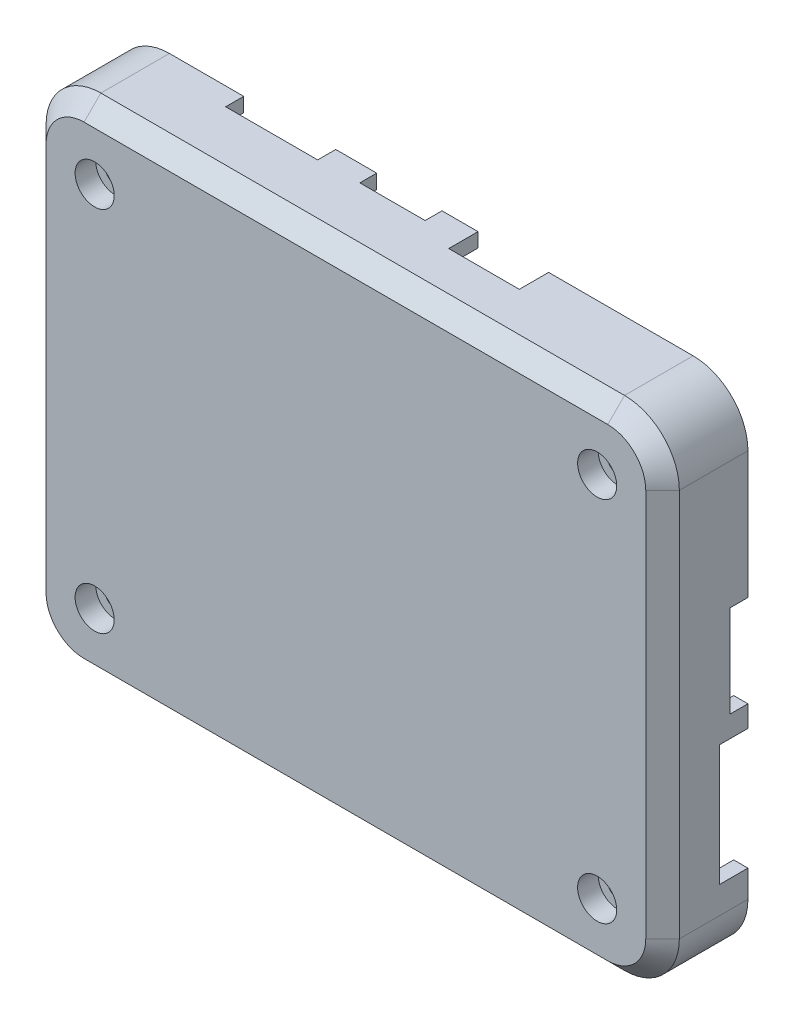
SolidWorks part; units mm, degrees
material "ABS"
ref_plane "前基準面" through (0, 0, 0) normal (0, 0, 1) x (1, 0, 0)
ref_plane "上基準面" through (0, 0, 0) normal (0, 1, 0) x (1, 0, 0)
ref_plane "右基準面" through (0, 0, 0) normal (1, 0, 0) x (0, 0, -1)
sketch "草圖1" plane through (0, 0, 0) normal (0, 0, 1) x (1, 0, 0)
  line L1 (-44.5, 35) -> (44.5, 35)
  line L2 (-44.5, 35) -> (-44.5, -35)
  line L3 (-44.5, -35) -> (44.5, -35)
  line L4 (44.5, 35) -> (44.5, -35)
  line L5 (-44.5, 35) -> (44.5, -35) construction
  line L6 (-44.5, -35) -> (44.5, 35) construction
  point P0 (0, 0)
  dimension "D1" = 89
  dimension "D2" = 70
extrude "填料-伸長1" add sketch "草圖1" along normal blind 12
fillet "圓角1" radius 7.7 4 edges at (-44.5, -35, 6) (44.5, -35, 6) (44.5, 35, 6) (-44.5, 35, 6)
chamfer "導角1" distance 2.36 angle 45 8 edges at (0, -35, 12) (42.2447, -32.7447, 12) (-42.2447, -32.7447, 12) (44.5, 0, 12) (-44.5, 0, 12) (42.2447, 32.7447, 12) (-42.2447, 32.7447, 12) (0, 35, 12)
shell "薄殼1" thickness 2
sketch "草圖2" plane through (0, 35, 0) normal (0, 1, 0) x (1, 0, 0)
  line L0 (36.8, 0) -> (-36.8, 0) construction
  line L1 (16.49, 0) -> (6.57, 0)
  line L2 (16.49, 0) -> (16.49, -4.12)
  line L3 (16.49, -4.12) -> (6.57, -4.12)
  line L4 (6.57, 0) -> (6.57, -4.12)
  line L5 (44.5, 0) -> (44.5, -9.64) construction
  line L6 (1.5, 0) -> (-7.67, 0)
  line L7 (1.5, 0) -> (1.5, -2.37)
  line L8 (1.5, -2.37) -> (-7.67, -2.37)
  line L9 (-7.67, 0) -> (-7.67, -2.37)
  line L10 (-13.43, 0) -> (-26.36, 0)
  line L11 (-13.43, 0) -> (-13.43, -2.54)
  line L12 (-13.43, -2.54) -> (-26.36, -2.54)
  line L13 (-26.36, 0) -> (-26.36, -2.54)
  point P16 (1.5, -1.185)
  dimension "D1" = 9.92
  dimension "D2" = 4.12
  dimension "D3" = 9.17
  dimension "D4" = 2.37
  dimension "D5" = 12.93
  dimension "D6" = 2.54
  dimension "D7" = 28.01
  dimension "D8" = 5.07
  dimension "D9" = 5.76
extrude "除料-伸長1" cut sketch "草圖2" against normal up to next
sketch "草圖3" plane through (44.5, 0, 0) normal (1, 0, 0) x (0, 0, -1)
  line L0 (0, -27.3) -> (0, 27.3) construction
  line L1 (0, 9.43) -> (-2.54, 9.43)
  line L2 (0, 9.43) -> (0, -3.5)
  line L3 (0, -3.5) -> (-2.54, -3.5)
  line L4 (-2.54, 9.43) -> (-2.54, -3.5)
  line L5 (0, -35) -> (-9.64, -35) construction
  line L6 (0, -6.5) -> (-4, -6.5)
  line L7 (0, -6.5) -> (0, -23.5)
  line L8 (0, -23.5) -> (-4, -23.5)
  line L9 (-4, -6.5) -> (-4, -23.5)
  dimension "D1" = 12.93
  dimension "D2" = 2.54
  dimension "D3" = 17
  dimension "D4" = 4
  dimension "D5" = 11.5
  dimension "D6" = 3
extrude "除料-伸長2" cut sketch "草圖3" against normal up to next
sketch "草圖4" plane through (-44.5, 0, 0) normal (-1, 0, 0) x (0, 0, 1)
  line L0 (0, 27.3) -> (0, -27.3) construction
  line L1 (0, -4.93) -> (2.54, -4.93)
  line L2 (0, -4.93) -> (0, 8)
  line L3 (0, 8) -> (2.54, 8)
  line L4 (2.54, -4.93) -> (2.54, 8)
  line L5 (0, 35) -> (9.64, 35) construction
  dimension "D1" = 12.93
  dimension "D2" = 2.54
  dimension "D3" = 27
extrude "除料-伸長3" cut sketch "草圖4" against normal up to next
sketch "草圖5" plane through (0, 0, 10) normal (0, 0, -1) x (-1, 0, 0)
  line L0 (-36.8, 31.8116) -> (36.8, 31.8116) construction
  line L1 (-41.3116, -27.3) -> (-41.3116, 27.3) construction
  line L2 (41.3116, 27.3) -> (41.3116, -27.3) construction
  line L3 (36.8, -31.8116) -> (-36.8, -31.8116) construction
  circle A0 centre (-35.3116, 25.8116) radius 4.5
  circle A1 centre (35.3116, 25.8116) radius 4.5
  circle A2 centre (35.3116, -25.8116) radius 4.5
  circle A4 centre (-35.3116, -25.8116) radius 4.5
  dimension "D3" = 9
  dimension "D1" = 6
  dimension "D2" = 6
  dimension "D4" = 6
  dimension "D5" = 6
  dimension "D6" = 6
extrude "填料-伸長2" add sketch "草圖5" along normal up to vertex (10 mm away)
hole_wizard "M2.5 六角承窩頭蓋螺釘的柱孔1" positions "3D草圖1" profile "草圖6" counterbore size "M2.5" standard "ISO" end condition through all
sketch3d "3D草圖1"
  circle A0 centre (35.3116, -25.8116, 0) radius 4.5 construction
  circle A1 centre (35.3116, 25.8116, 0) radius 4.5 construction
  circle A2 centre (-35.3116, 25.8116, 0) radius 4.5 construction
  circle A3 centre (-35.3116, -25.8116, 0) radius 4.5 construction
  point P0 (35.3116, -25.8116, 12)
  point P9 (35.3116, -25.8116, -4.5)
  point P10 (-35.3116, -25.8116, 12)
  point P12 (-35.3116, 25.8116, 12)
  point P14 (35.3116, 25.8116, 12)
  point P19 (35.3116, 25.8116, -4.5)
  point P22 (-35.3116, 25.8116, -4.5)
  point P25 (-35.3116, -25.8116, -4.5)
sketch "草圖6" plane through (35.3116, -25.8116, 12) normal (1, 0, 0) x (0, -1, 0)
  line L0 (0, 0) -> (0, 12)
  line L1 (0, 12) -> (1.45, 12)
  line L3 (1.45, 12) -> (1.45, 2.9)
  line L4 (1.45, 2.9) -> (2.75, 2.9)
  line L5 (2.75, 2.9) -> (2.75, 0)
  line L7 (2.75, 0) -> (0, 0)
  line L11 (0, -6.35) -> (0, 107.95) construction
  dimension "貫穿孔直徑" = 2.9
  dimension "貫穿孔深度" = 12
  dimension "柱孔直徑" = 5.5
  dimension "柱孔深度" = 2.9
